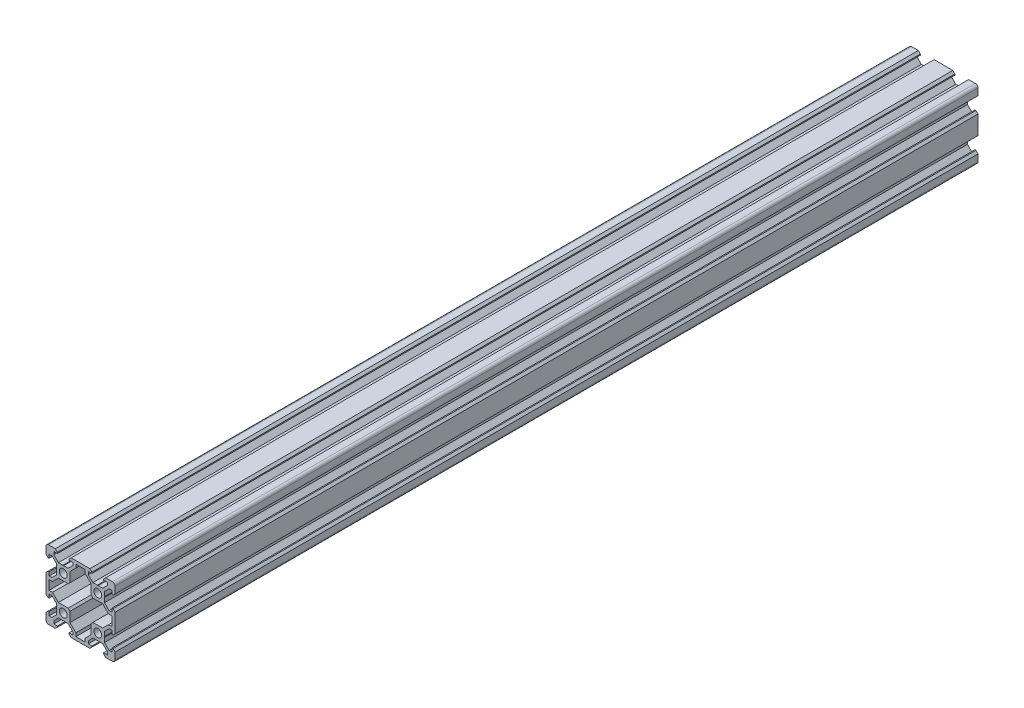
SolidWorks part; units mm, degrees
material "6061-T6 (SS)"
ref_plane "Front Plane" through (0, 0, 0) normal (0, 0, 1) x (1, 0, 0)
ref_plane "Top Plane" through (0, 0, 0) normal (0, 1, 0) x (1, 0, 0)
ref_plane "Right Plane" through (0, 0, 0) normal (1, 0, 0) x (0, 0, -1)
sketch "Sketch1" plane through (0, 0, 0) normal (0, 0, 1) x (1, 0, 0)
  line L1 (18.5, -20) -> (-18.5, -20)
  line L2 (20, -18.5) -> (20, 18.5)
  line L3 (18.5, 20) -> (-18.5, 20)
  line L4 (-20, -18.5) -> (-20, 18.5)
  line L5 (20, -20) -> (-20, 20) construction
  line L6 (20, 20) -> (-20, -20) construction
  circle A0 centre (-10, 10) radius 2.3
  circle A1 centre (10, -10) radius 2.3
  circle A2 centre (10, 10) radius 2.3
  circle A3 centre (-10, -10) radius 2.3
  arc A4 (-18.5, -20) -> (-20, -18.5) centre (-18.5, -18.5) cw
  arc A5 (18.5, -20) -> (20, -18.5) centre (18.5, -18.5) ccw
  arc A6 (20, 18.5) -> (18.5, 20) centre (18.5, 18.5) ccw
  arc A7 (-18.5, 20) -> (-20, 18.5) centre (-18.5, 18.5) ccw
  point P0 (0, 0)
  line B0 (-10, 10) -> (-10, 20) construction
  line B1 (-10, 13.69) -> (-10.21, 13.9)
  line B2 (-10.21, 13.9) -> (-12.8393, 13.9)
  line B3 (-12.8393, 13.9) -> (-15.5, 16.5607)
  line B4 (-15.5, 16.5607) -> (-15.5, 18.2)
  line B5 (-15.5, 18.2) -> (-13.395, 18.2)
  line B6 (-13.395, 18.2) -> (-13.395, 18.815)
  line B7 (-13.395, 18.815) -> (-14.58, 20)
  line B8 (-14.58, 20) -> (-5.42, 20)
  line B9 (-10, 10) -> (-15.9132, 15.9132) construction
  line B10 (-6.605, 18.815) -> (-5.42, 20)
  line B11 (-6.605, 18.2) -> (-6.605, 18.815)
  line B12 (-4.5, 18.2) -> (-6.605, 18.2)
  line B13 (-4.5, 16.5607) -> (-4.5, 18.2)
  line B14 (-7.1607, 13.9) -> (-4.5, 16.5607)
  line B15 (-9.79, 13.9) -> (-7.1607, 13.9)
  line B16 (-10, 13.69) -> (-9.79, 13.9)
  line B17 (10, 10) -> (10, 20) construction
  line B18 (10, 13.69) -> (9.79, 13.9)
  line B19 (9.79, 13.9) -> (7.1607, 13.9)
  line B20 (7.1607, 13.9) -> (4.5, 16.5607)
  line B21 (4.5, 16.5607) -> (4.5, 18.2)
  line B22 (4.5, 18.2) -> (6.605, 18.2)
  line B23 (6.605, 18.2) -> (6.605, 18.815)
  line B24 (6.605, 18.815) -> (5.42, 20)
  line B25 (5.42, 20) -> (14.58, 20)
  line B26 (10, 10) -> (4.0868, 15.9132) construction
  line B27 (13.395, 18.815) -> (14.58, 20)
  line B28 (13.395, 18.2) -> (13.395, 18.815)
  line B29 (15.5, 18.2) -> (13.395, 18.2)
  line B30 (15.5, 16.5607) -> (15.5, 18.2)
  line B31 (12.8393, 13.9) -> (15.5, 16.5607)
  line B32 (10.21, 13.9) -> (12.8393, 13.9)
  line B33 (10, 13.69) -> (10.21, 13.9)
  line B34 (-10, 10) -> (-20, 10) construction
  line B35 (-13.69, 10) -> (-13.9, 9.79)
  line B36 (-13.9, 9.79) -> (-13.9, 7.1607)
  line B37 (-13.9, 7.1607) -> (-16.5607, 4.5)
  line B38 (-16.5607, 4.5) -> (-18.2, 4.5)
  line B39 (-18.2, 4.5) -> (-18.2, 6.605)
  line B40 (-18.2, 6.605) -> (-18.815, 6.605)
  line B41 (-18.815, 6.605) -> (-20, 5.42)
  line B42 (-20, 5.42) -> (-20, 14.58)
  line B43 (-10, 10) -> (-15.9132, 4.0868) construction
  line B44 (-18.815, 13.395) -> (-20, 14.58)
  line B45 (-18.2, 13.395) -> (-18.815, 13.395)
  line B46 (-18.2, 15.5) -> (-18.2, 13.395)
  line B47 (-16.5607, 15.5) -> (-18.2, 15.5)
  line B48 (-13.9, 12.8393) -> (-16.5607, 15.5)
  line B49 (-13.9, 10.21) -> (-13.9, 12.8393)
  line B50 (-13.69, 10) -> (-13.9, 10.21)
  line B51 (-10, -10) -> (-20, -10) construction
  line B52 (-13.69, -10) -> (-13.9, -10.21)
  line B53 (-13.9, -10.21) -> (-13.9, -12.8393)
  line B54 (-13.9, -12.8393) -> (-16.5607, -15.5)
  line B55 (-16.5607, -15.5) -> (-18.2, -15.5)
  line B56 (-18.2, -15.5) -> (-18.2, -13.395)
  line B57 (-18.2, -13.395) -> (-18.815, -13.395)
  line B58 (-18.815, -13.395) -> (-20, -14.58)
  line B59 (-20, -14.58) -> (-20, -5.42)
  line B60 (-10, -10) -> (-15.9132, -15.9132) construction
  line B61 (-18.815, -6.605) -> (-20, -5.42)
  line B62 (-18.2, -6.605) -> (-18.815, -6.605)
  line B63 (-18.2, -4.5) -> (-18.2, -6.605)
  line B64 (-16.5607, -4.5) -> (-18.2, -4.5)
  line B65 (-13.9, -7.1607) -> (-16.5607, -4.5)
  line B66 (-13.9, -9.79) -> (-13.9, -7.1607)
  line B67 (-13.69, -10) -> (-13.9, -9.79)
  line B68 (-10, -10) -> (-10, -20) construction
  line B69 (-10, -13.69) -> (-9.79, -13.9)
  line B70 (-9.79, -13.9) -> (-7.1607, -13.9)
  line B71 (-7.1607, -13.9) -> (-4.5, -16.5607)
  line B72 (-4.5, -16.5607) -> (-4.5, -18.2)
  line B73 (-4.5, -18.2) -> (-6.605, -18.2)
  line B74 (-6.605, -18.2) -> (-6.605, -18.815)
  line B75 (-6.605, -18.815) -> (-5.42, -20)
  line B76 (-5.42, -20) -> (-14.58, -20)
  line B77 (-10, -10) -> (-4.0868, -15.9132) construction
  line B78 (-13.395, -18.815) -> (-14.58, -20)
  line B79 (-13.395, -18.2) -> (-13.395, -18.815)
  line B80 (-15.5, -18.2) -> (-13.395, -18.2)
  line B81 (-15.5, -16.5607) -> (-15.5, -18.2)
  line B82 (-12.8393, -13.9) -> (-15.5, -16.5607)
  line B83 (-10.21, -13.9) -> (-12.8393, -13.9)
  line B84 (-10, -13.69) -> (-10.21, -13.9)
  line B85 (10, -10) -> (10, -20) construction
  line B86 (10, -13.69) -> (10.21, -13.9)
  line B87 (10.21, -13.9) -> (12.8393, -13.9)
  line B88 (12.8393, -13.9) -> (15.5, -16.5607)
  line B89 (15.5, -16.5607) -> (15.5, -18.2)
  line B90 (15.5, -18.2) -> (13.395, -18.2)
  line B91 (13.395, -18.2) -> (13.395, -18.815)
  line B92 (13.395, -18.815) -> (14.58, -20)
  line B93 (14.58, -20) -> (5.42, -20)
  line B94 (10, -10) -> (15.9132, -15.9132) construction
  line B95 (6.605, -18.815) -> (5.42, -20)
  line B96 (6.605, -18.2) -> (6.605, -18.815)
  line B97 (4.5, -18.2) -> (6.605, -18.2)
  line B98 (4.5, -16.5607) -> (4.5, -18.2)
  line B99 (7.1607, -13.9) -> (4.5, -16.5607)
  line B100 (9.79, -13.9) -> (7.1607, -13.9)
  line B101 (10, -13.69) -> (9.79, -13.9)
  line B102 (10, 10) -> (20, 10) construction
  line B103 (13.69, 10) -> (13.9, 10.21)
  line B104 (13.9, 10.21) -> (13.9, 12.8393)
  line B105 (13.9, 12.8393) -> (16.5607, 15.5)
  line B106 (16.5607, 15.5) -> (18.2, 15.5)
  line B107 (18.2, 15.5) -> (18.2, 13.395)
  line B108 (18.2, 13.395) -> (18.815, 13.395)
  line B109 (18.815, 13.395) -> (20, 14.58)
  line B110 (20, 14.58) -> (20, 5.42)
  line B111 (10, 10) -> (15.9132, 15.9132) construction
  line B112 (18.815, 6.605) -> (20, 5.42)
  line B113 (18.2, 6.605) -> (18.815, 6.605)
  line B114 (18.2, 4.5) -> (18.2, 6.605)
  line B115 (16.5607, 4.5) -> (18.2, 4.5)
  line B116 (13.9, 7.1607) -> (16.5607, 4.5)
  line B117 (13.9, 9.79) -> (13.9, 7.1607)
  line B118 (13.69, 10) -> (13.9, 9.79)
  line B119 (10, -10) -> (20, -10) construction
  line B120 (13.69, -10) -> (13.9, -9.79)
  line B121 (13.9, -9.79) -> (13.9, -7.1607)
  line B122 (13.9, -7.1607) -> (16.5607, -4.5)
  line B123 (16.5607, -4.5) -> (18.2, -4.5)
  line B124 (18.2, -4.5) -> (18.2, -6.605)
  line B125 (18.2, -6.605) -> (18.815, -6.605)
  line B126 (18.815, -6.605) -> (20, -5.42)
  line B127 (20, -5.42) -> (20, -14.58)
  line B128 (10, -10) -> (15.9132, -4.0868) construction
  line B129 (18.815, -13.395) -> (20, -14.58)
  line B130 (18.2, -13.395) -> (18.815, -13.395)
  line B131 (18.2, -15.5) -> (18.2, -13.395)
  line B132 (16.5607, -15.5) -> (18.2, -15.5)
  line B133 (13.9, -12.8393) -> (16.5607, -15.5)
  line B134 (13.9, -10.21) -> (13.9, -12.8393)
  line B135 (13.69, -10) -> (13.9, -10.21)
  line B136 (-18.2, -2.7) -> (-18.2, 2.7)
  line B137 (-18.2, 2.7) -> (-16.2393, 2.7)
  line B138 (-16.2393, 2.7) -> (-12.8393, 6.1)
  line B139 (-12.8393, 6.1) -> (-7.1607, 6.1)
  line B140 (-10, 6.1) -> (-10, 0) construction
  line B141 (-10, 0) -> (-18.2, 0) construction
  line B142 (-12.8393, -6.1) -> (-7.1607, -6.1)
  line B143 (-16.2393, -2.7) -> (-12.8393, -6.1)
  line B144 (-18.2, -2.7) -> (-16.2393, -2.7)
  line B145 (-10, 6.1) -> (-10, 10) construction
  line B146 (-10, 10) -> (-15.0927, 4.9073) construction
  line B147 (-10, 10) -> (-6.3747, 6.3747) construction
  line B148 (2.7, 18.2) -> (2.7, 16.2393)
  line B149 (2.7, 16.2393) -> (6.1, 12.8393)
  line B150 (6.1, 12.8393) -> (6.1, 7.1607)
  line B151 (-6.1, 12.8393) -> (-6.1, 7.1607)
  line B152 (-2.7, 16.2393) -> (-6.1, 12.8393)
  line B153 (-2.7, 18.2) -> (-2.7, 16.2393)
  line B154 (2.7, 18.2) -> (-2.7, 18.2)
  line B155 (2.7, -18.2) -> (-2.7, -18.2)
  line B156 (-2.7, -18.2) -> (-2.7, -16.2393)
  line B157 (-2.7, -16.2393) -> (-6.1, -12.8393)
  line B158 (-6.1, -12.8393) -> (-6.1, -7.1607)
  line B159 (6.1, -12.8393) -> (6.1, -7.1607)
  line B160 (2.7, -16.2393) -> (6.1, -12.8393)
  line B161 (2.7, -18.2) -> (2.7, -16.2393)
  line B162 (0, 18.2) -> (0, -18.2) construction
  line B163 (12.8393, -6.1) -> (7.1607, -6.1)
  line B164 (16.2393, -2.7) -> (12.8393, -6.1)
  line B165 (18.2, -2.7) -> (16.2393, -2.7)
  line B166 (18.2, -2.7) -> (18.2, 2.7)
  line B167 (18.2, 2.7) -> (16.2393, 2.7)
  line B168 (16.2393, 2.7) -> (12.8393, 6.1)
  line B169 (12.8393, 6.1) -> (7.1607, 6.1)
  line B170 (-7.1607, 6.1) -> (-6.1, 7.1607)
  line B171 (6.1, 7.1607) -> (7.1607, 6.1)
  line B172 (7.1607, -6.1) -> (6.1, -7.1607)
  line B173 (-6.1, -7.1607) -> (-7.1607, -6.1)
  dimension "D4" = 4.6
  dimension "D5" = 1.5
  dimension "D1" = 40
  dimension "D2" = 10
  dimension "D3" = 10
sketch_block_instance "V Slot 2-1"
sketch_block "V Slot 2" parameters "D1"=10, "D2"=11, "D3"=4.3, "D4"=1.8, "D5"=0.21, "D6"=45, "D7"=9.16, "D8"=1.5, "D9"=6.79
sketch_block_instance "V Slot 2-2"
sketch_block_instance "V Slot 2-3"
sketch_block_instance "V Slot 2-4"
sketch_block_instance "V Slot 2-5"
sketch_block_instance "V Slot 2-6"
sketch_block_instance "V Slot 2-7"
sketch_block_instance "V Slot 2-8"
sketch_block_instance "Center Cutout 2-1"
sketch_block "Center Cutout 2" parameters "D1"=5.4, "D2"=12.2, "D3"=8.2, "D4"=45, "D5"=10, "D6"=1.5
extrude "Boss-Extrude1" add sketch "Sketch1" along normal blind 500 contours B135 B120 B121 B122 B123 B124 B125 B126 L2 B112 B113 B114 B115 B116 B117 B118 B103 B104 B105 B106 B107 B108 B109 A6 L3 B27 B28 B29 B30 B31 B32 B33 B18 B19 B20 B21 B22 B23 B24 B10 B11 B12 B13 B14 B15 B16 B1 B2 B3
